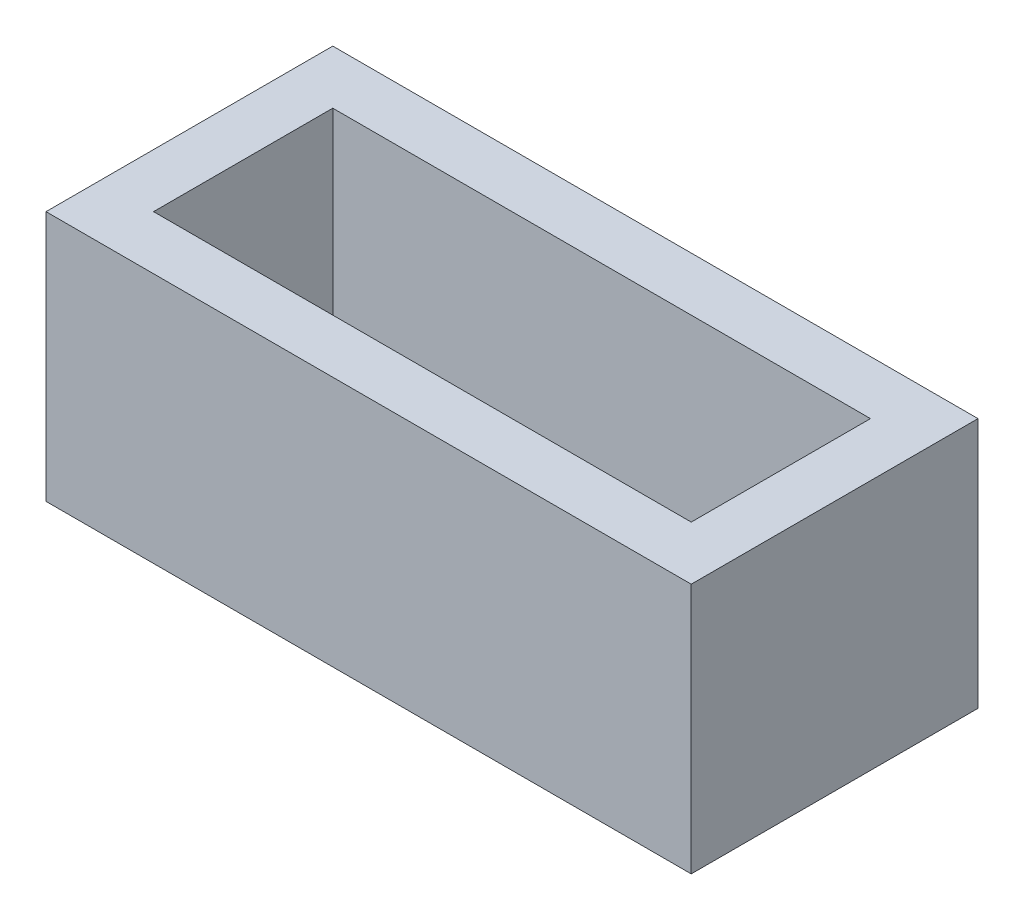
SolidWorks part; units mm, degrees
ref_plane "Front Plane" through (0, 0, 0) normal (0, 0, 1) x (1, 0, 0)
ref_plane "Top Plane" through (0, 0, 0) normal (0, 1, 0) x (1, 0, 0)
ref_plane "Right Plane" through (0, 0, 0) normal (1, 0, 0) x (0, 0, -1)
sketch "Sketch1" plane through (0, 0, 0) normal (0, 1, 0) x (1, 0, 0)
  line L0 (30, 130) -> (330, 130)
  line L1 (0, 0) -> (360, 0)
  line L2 (0, 0) -> (0, 160)
  line L3 (0, 160) -> (360, 160)
  line L4 (360, 0) -> (360, 160)
  line L5 (330, 30) -> (330, 130)
  line L6 (30, 30) -> (330, 30)
  line L7 (30, 30) -> (30, 130)
  dimension "D1" = 360
  dimension "D2" = 160
  dimension "D3" = 30
extrude "Boss-Extrude1" add sketch "Sketch1" along normal blind 140
